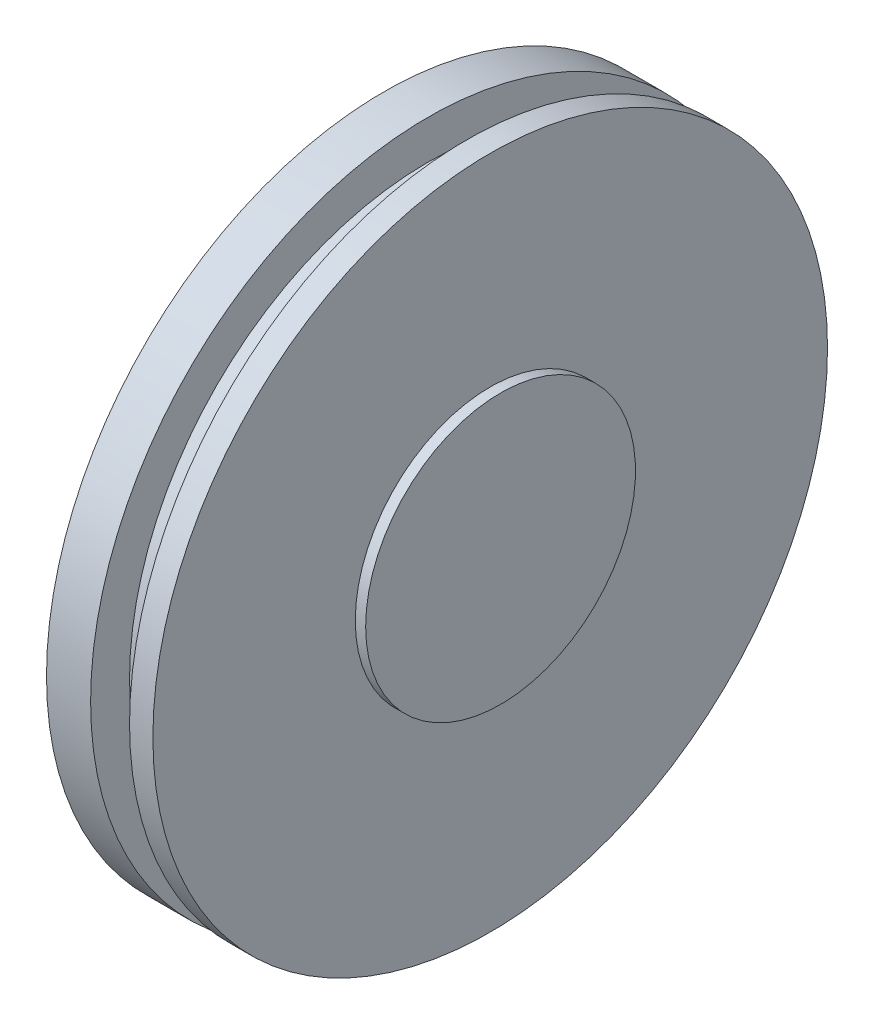
SolidWorks part; units mm, degrees
ref_plane "Face" through (0, 0, 0) normal (0, 0, 1) x (1, 0, 0)
ref_plane "Dessus" through (0, 0, 0) normal (0, 1, 0) x (1, 0, 0)
ref_plane "Droite" through (0, 0, 0) normal (1, 0, 0) x (0, 0, -1)
sketch "Esquisse1" plane through (0, 0, 0) normal (0, 0, 1) x (1, 0, 0)
  line L0 (-0.4, 13) -> (-1.3, 13)
  line L1 (-4.5, 13) -> (-4.5, 0)
  line L2 (-1.3, 13) -> (-1.3, 11.5)
  line L3 (-2.8, 13) -> (-2.8, 11.5)
  line L4 (-2.8, 11.5) -> (-1.3, 11.5)
  line L5 (-0.4, 13) -> (-0.4, 5.2)
  line L6 (-0.4, 5.2) -> (0, 5.2)
  line L7 (0, 5.2) -> (0, 0)
  line L8 (-3.7452, 0) -> (3.882, 0) construction
  line L9 (-2.8, 13) -> (-4.5, 13)
  line L10 (-4.5, 0) -> (0, 0)
  dimension "D1" = 2.8
  dimension "D2" = 1.5
  dimension "D3" = 11.5
  dimension "D4" = 13
  dimension "D5" = 0.4
  dimension "D6" = 1.7
  dimension "D7" = 5.2
revolve "Base-Révolution" add sketch "Esquisse1" angle 360 about L8
